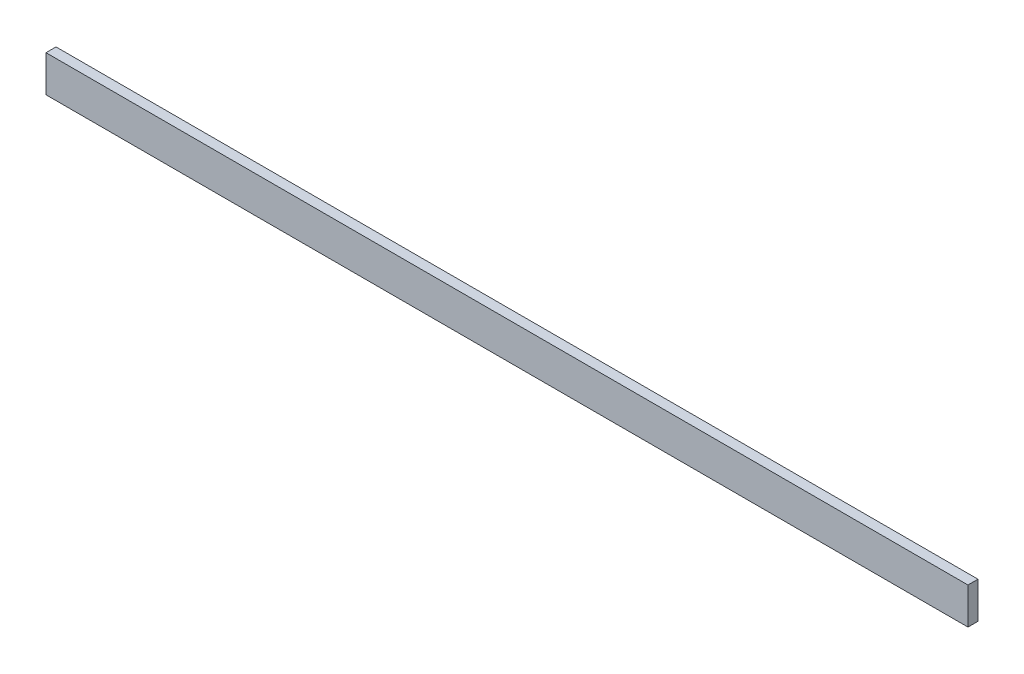
SolidWorks part; units mm, degrees
ref_plane "Plan de face" through (0, 0, 0) normal (0, 0, 1) x (1, 0, 0)
ref_plane "Plan de dessus" through (0, 0, 0) normal (0, 1, 0) x (1, 0, 0)
ref_plane "Plan de droite" through (0, 0, 0) normal (1, 0, 0) x (0, 0, -1)
sketch "Esquisse1" plane through (0, 0, 0) normal (0, 0, 1) x (1, 0, 0)
  line L1 (0, 0) -> (2022, 0)
  line L2 (0, 0) -> (0, 80)
  line L3 (0, 80) -> (2022, 80)
  line L4 (2022, 0) -> (2022, 80)
  dimension "D1" = 2022
  dimension "D2" = 80
extrude "Extrusion1" add sketch "Esquisse1" along normal blind 22
